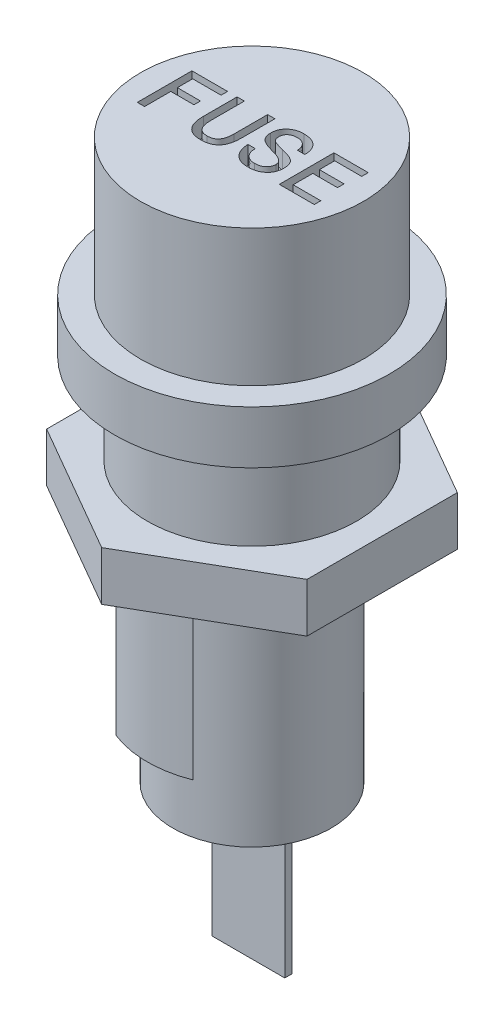
SolidWorks part; units mm, degrees
ref_plane "Front Plane" through (0, 0, 0) normal (0, 0, 1) x (1, 0, 0)
ref_plane "Top Plane" through (0, 0, 0) normal (0, 1, 0) x (1, 0, 0)
ref_plane "Right Plane" through (0, 0, 0) normal (1, 0, 0) x (0, 0, -1)
sketch "Sketch1" plane through (0, 0, 0) normal (0, 1, 0) x (1, 0, 0)
  circle A0 centre (0, 0) radius 5.75
  dimension "D1" = 11.5
extrude "Boss-Extrude1" add sketch "Sketch1" along normal blind 7.7
sketch "Sketch2" plane through (0, 0, 0) normal (0, -1, 0) x (1, 0, 0)
  circle A0 centre (0, 0) radius 4.35
  dimension "D1" = 8.7
extrude "Boss-Extrude2" add sketch "Sketch2" along normal blind 12.6
sketch "Sketch3" plane through (0, 7.7, 0) normal (0, 1, 0) x (1, 0, 0)
  circle A0 centre (0, 0) radius 7.55
  dimension "D1" = 15.1
extrude "Boss-Extrude3" add sketch "Sketch3" along normal blind 2.9
sketch "Sketch4" plane through (0, 10.6, 0) normal (0, 1, 0) x (1, 0, 0)
  circle A0 centre (0, 0) radius 6.125
  dimension "D1" = 12.25
extrude "Boss-Extrude4" add sketch "Sketch4" along normal blind 7.5
sketch "Sketch5" plane through (0, 18.1, 0) normal (0, 1, 0) x (1, 0, 0)
  line L0 (-5.9385, -1.5) -> (5.9385, -1.5) construction
  circle A0 centre (0, 0) radius 6.125 construction
  text T0 "FUSE" font "Monospac821 BT" height 3
  point P5 (0, 0)
  dimension "D1" = 1.5
extrude "Cut-Extrude1" cut sketch "Sketch5" against normal blind 1
sketch "Sketch6" plane through (0, 0, 0) normal (0, -1, 0) x (1, 0, 0)
  line L1 (-7.15, 4.1281) -> (-7.15, -4.1281)
  line L2 (-7.15, -4.1281) -> (0, -8.2561)
  line L3 (0, -8.2561) -> (7.15, -4.1281)
  line L4 (7.15, -4.1281) -> (7.15, 4.1281)
  line L5 (7.15, 4.1281) -> (0, 8.2561)
  line L6 (0, 8.2561) -> (-7.15, 4.1281)
  circle A0 centre (0, 0) radius 5.75
  circle A1 centre (0, 0) radius 5.75 construction
  circle A2 centre (0, 0) radius 7.15 construction
  point P5 (-8.0435, 3.4641)
  point P13 (-8.6198, 4.9767)
  dimension "D1" = 14.3
extrude "Boss-Extrude5" add sketch "Sketch6" against normal blind 2.7 separate body
sketch "Sketch7" plane through (0, -12.6, 0) normal (0, -1, 0) x (1, 0, 0)
  line L1 (-2, -0.2) -> (2, -0.2)
  line L2 (-2, -0.2) -> (-2, 0.2)
  line L3 (-2, 0.2) -> (2, 0.2)
  line L4 (2, -0.2) -> (2, 0.2)
  line L5 (-2, -0.2) -> (2, 0.2) construction
  line L6 (-2, 0.2) -> (2, -0.2) construction
  point P0 (0, 0)
  dimension "D1" = 4
  dimension "D2" = 0.4
extrude "Boss-Extrude6" add sketch "Sketch7" along normal blind 8.2
sketch "Sketch8" plane through (0, 0, 0) normal (0, -1, 0) x (1, 0, 0)
  line L0 (-2.1071, 5.35) -> (2.1071, 5.35)
  line L1 (0, 5.75) -> (0, 5.35) construction
  circle A0 centre (0, 0) radius 5.75 construction
  circle A1 centre (0, 0) radius 5.75 construction
  arc A2 (2.1071, 5.35) -> (-2.1071, 5.35) centre (0, 0) ccw
  dimension "D1" = 0.4
extrude "Boss-Extrude7" add sketch "Sketch8" along normal blind 8.75
